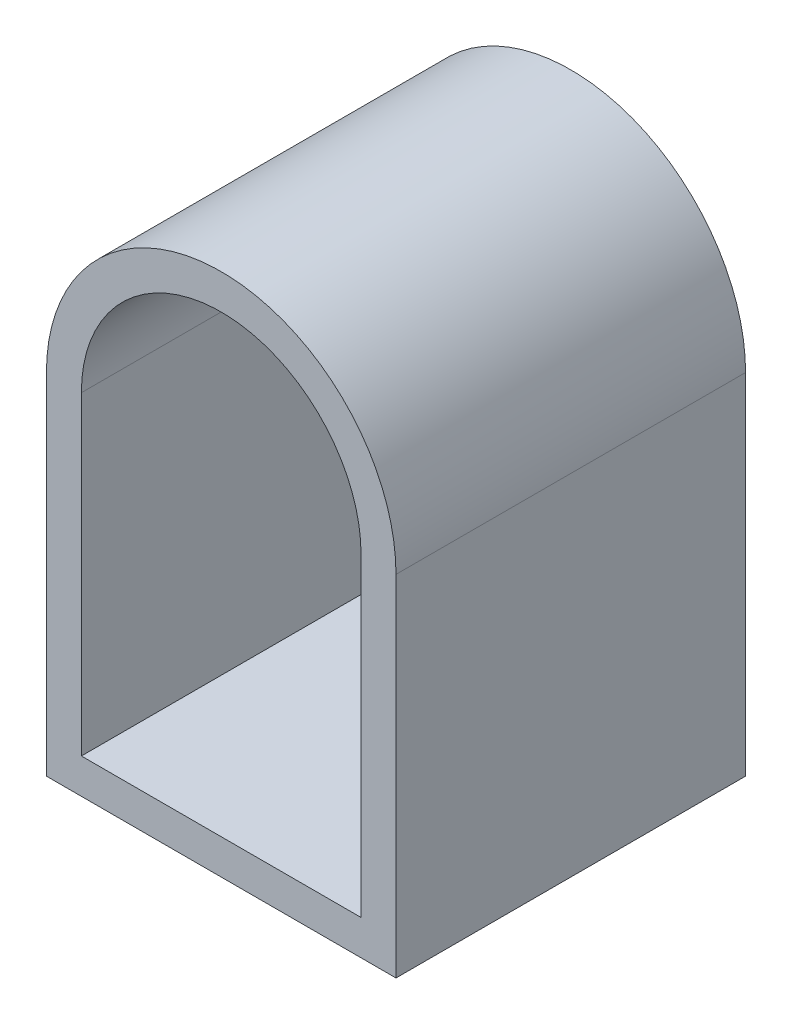
SolidWorks part; units mm, degrees
ref_plane "Front Plane" through (0, 0, 0) normal (0, 0, 1) x (1, 0, 0)
ref_plane "Top Plane" through (0, 0, 0) normal (0, 1, 0) x (1, 0, 0)
ref_plane "Right Plane" through (0, 0, 0) normal (1, 0, 0) x (0, 0, -1)
sketch "Sketch1" plane through (0, 0, 0) normal (0, 0, 1) x (1, 0, 0)
  line L0 (0, 0) -> (0, 12.7)
  line L1 (12.7, 12.7) -> (12.7, 0)
  line L2 (12.7, 0) -> (0, 0)
  line L3 (1.27, 1.27) -> (11.43, 1.27)
  line L4 (11.43, 1.27) -> (11.43, 12.7)
  line L5 (1.27, 12.7) -> (1.27, 1.27)
  arc A0 (0, 12.7) -> (12.7, 12.7) centre (6.35, 12.7) cw
  arc A1 (11.43, 12.7) -> (1.27, 12.7) centre (6.35, 12.7) ccw
  point P11 (0, 0)
  dimension "D2" = 6.35
  dimension "D3" = 5.08
  dimension "D1" = 12.7
  dimension "D4" = 11.43
extrude "Boss-Extrude1" add sketch "Sketch1" along normal blind 12.7
